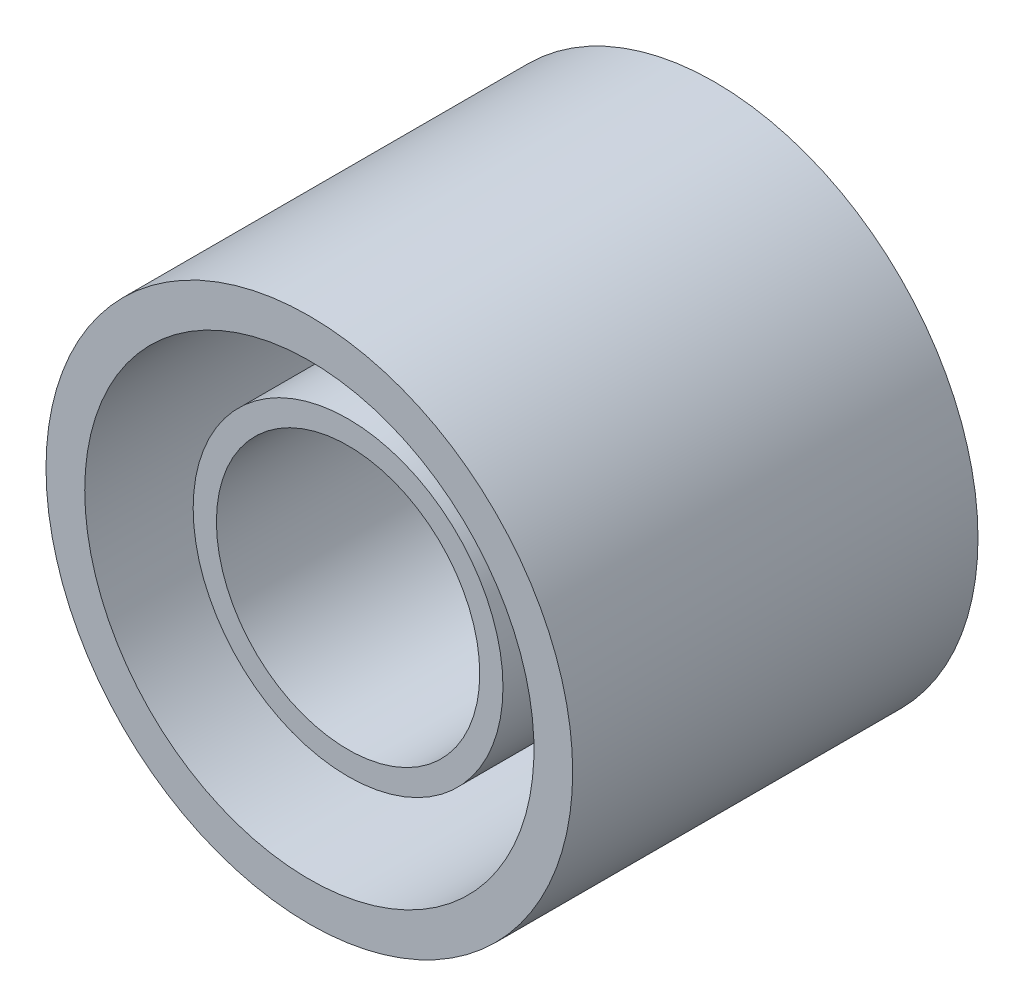
SolidWorks part; units mm, degrees
material "Alumina"
ref_plane "Front Plane" through (0, 0, 0) normal (0, 0, 1) x (1, 0, 0)
ref_plane "Top Plane" through (0, 0, 0) normal (0, 1, 0) x (1, 0, 0)
ref_plane "Right Plane" through (0, 0, 0) normal (1, 0, 0) x (0, 0, -1)
ref_plane "Plane1" through (259.3015, 0, 0) normal (-1, 0, 0) x (0, 0, 1)
sketch "Sketch2" plane through (259.3015, 0, 0) normal (-1, 0, 0) x (0, 0, 1)
  line L0 (0, -133.5737) -> (5, -133.5737)
  line L1 (5, -133.5737) -> (5, -131.5737)
  line L2 (5, -119.5737) -> (52.3305, -119.5737)
  line L3 (52.3305, -119.5737) -> (52.3305, -114.5737)
  line L4 (52.3305, -114.5737) -> (0, -114.5737)
  line L5 (0, -114.5737) -> (0, -133.5737)
  line L6 (-1.12, -148.5737) -> (64.0146, -148.5737) construction
  line L7 (5, -133.5737) -> (0, -133.5737) construction
  line L8 (5, -128.5737) -> (5, -119.5737)
  line L9 (5, -128.5737) -> (47.3305, -128.5737)
  line L11 (5, -131.5737) -> (47.3305, -131.5737)
  line L12 (47.3305, -128.5737) -> (47.3305, -131.5737)
  point P15 (52.3305, -117.0737)
  dimension "D1" = 29
  dimension "D2" = 0
  dimension "D3" = 5
  dimension "D4" = 5
  dimension "D5" = 5
  dimension "D7" = 17
  dimension "D6" = 20
  dimension "D8" = 47.3305
revolve "Revolve1" add sketch "Sketch2" angle 360 about L6
equation "\"D1@Sketch2\" = \"External_OR@Thruster_Assembly.Assembly\""
equation "\"D7@Sketch2\"=\"External_IR@Thruster_Assembly.Assembly\"-6"
equation "\"D6@Sketch2\"=\"External_IR@Thruster_Assembly.Assembly\"-3"
